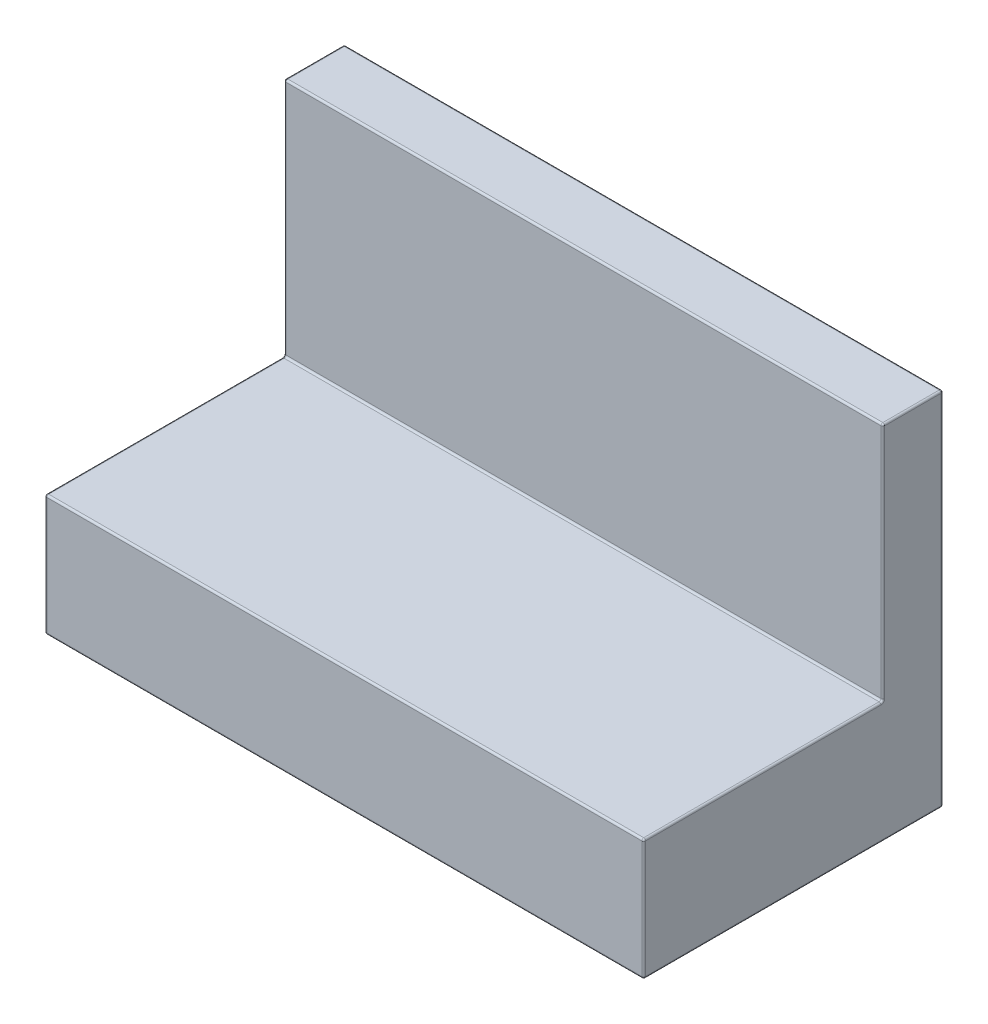
SolidWorks part; units mm, degrees
ref_plane "Front Plane" through (0, 0, 0) normal (0, 0, 1) x (1, 0, 0)
ref_plane "Top Plane" through (0, 0, 0) normal (0, 1, 0) x (1, 0, 0)
ref_plane "Right Plane" through (0, 0, 0) normal (1, 0, 0) x (0, 0, -1)
sketch "Sketch1" plane through (0, 0, 0) normal (0, 1, 0) x (1, 0, 0)
  line L1 (-3.98, 3.98) -> (3.98, 3.98)
  line L2 (-3.98, 3.98) -> (-3.98, -3.98)
  line L3 (-3.98, -3.98) -> (3.98, -3.98)
  line L4 (3.98, 3.98) -> (3.98, -3.98)
  line L5 (-3.98, 3.98) -> (3.98, -3.98) construction
  line L6 (-3.98, -3.98) -> (3.98, 3.98) construction
  point P0 (0, 0)
  dimension "D1" = 7.96
extrude "Extrude1" add sketch "Sketch1" along normal blind 3.22
pattern_linear "LPattern1" count 2 spacing 7.96 along (1, 0, 0) of "Extrude1"
shell "Shell1" thickness 1.55
sketch "Sketch4" plane through (0, 1.67, 0) normal (0, -1, 0) x (1, 0, 0)
  line L0 (10.39, 2.43) -> (10.39, -2.43) construction
  line L1 (-2.43, 2.43) -> (10.39, 2.43) construction
  line L2 (-2.43, -2.43) -> (-2.43, 2.43) construction
  line L3 (10.39, -2.43) -> (-2.43, -2.43) construction
  line L4 (10.39, 2.43) -> (10.39, -2.43)
  line L5 (-2.43, 2.43) -> (10.39, 2.43)
  line L6 (-2.43, -2.43) -> (-2.43, 2.43)
  line L7 (10.39, -2.43) -> (-2.43, -2.43)
extrude "Extrude3" cut sketch "Sketch4" against normal blind 0.14
sketch "Sketch5" plane through (0, 1.81, 0) normal (0, -1, 0) x (1, 0, 0)
  line L0 (10.39, 2.43) -> (-2.43, 2.43) construction
  circle A0 centre (3.98, 0) radius 1.5
  circle A1 centre (3.98, 0) radius 0.64
  point P5 (3.98, 2.43)
  dimension "D1" = 3
  dimension "D2" = 0.86
extrude "Extrude4" add sketch "Sketch5" along normal up to surface (1.81 mm away) up to face at (3.98, 0, 0)
sketch "Sketch6" plane through (0, 3.22, 0) normal (0, 1, 0) x (1, 0, 0)
  line L0 (11.94, -3.98) -> (11.94, 3.98) construction
  line L1 (-3.98, 3.98) -> (11.94, 3.98)
  line L2 (-3.98, 3.98) -> (-3.98, 2.38)
  line L3 (-3.98, 2.38) -> (11.94, 2.38)
  line L4 (11.94, 3.98) -> (11.94, 2.38)
  dimension "D1" = 1.6
extrude "Extrude5" add sketch "Sketch6" along normal blind 6.38
fillet "Fillet1" radius 0.05 34 edges at (-3.98, 9.6, -3.18) (3.98, 9.6, -2.38) (11.94, 9.6, -3.18) (3.98, 9.6, -3.98) (3.98, 1.81, -0.64) (3.98, 0, 1.5) (3.98, 0, 0.64) (3.98, 1.81, 2.43) (-2.43, 1.81, 0) (3.98, 1.81, -2.43) (10.39, 1.81, 0) (10.39, 0, 0) (10.39, 0.905, 2.43) (10.39, 0.905, -2.43) (3.98, 0, -2.43) (-2.43, 0, 0) (3.98, 0, 2.43) (-2.43, 0.905, 2.43) (-2.43, 0.905, -2.43) (11.94, 0, 0) (11.94, 1.61, 3.98) (11.94, 4.8, -3.98) (3.98, 0, -3.98) (-3.98, 0, 0) (3.98, 0, 3.98) (3.98, 3.22, 3.98) (-3.98, 1.61, 3.98) (-3.98, 4.8, -3.98) (3.98, 1.81, 1.5)
